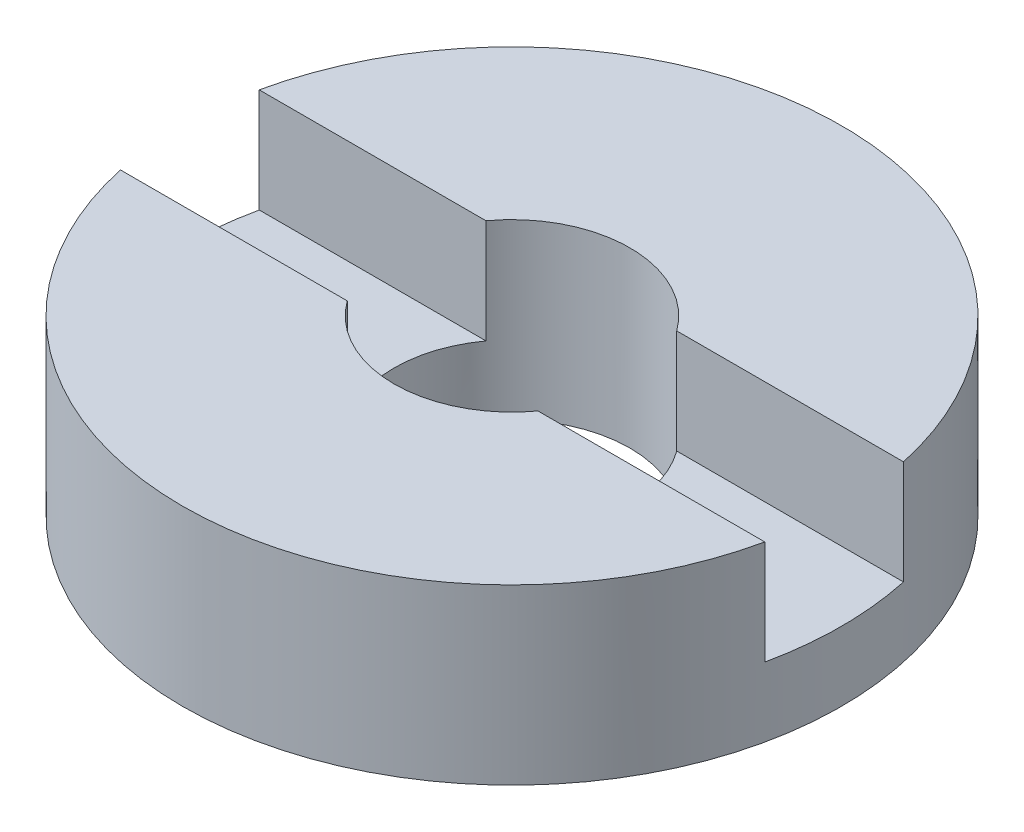
SolidWorks part; units mm, degrees
ref_plane "前视基准面" through (0, 0, 0) normal (0, 0, 1) x (1, 0, 0)
ref_plane "上视基准面" through (0, 0, 0) normal (0, 1, 0) x (1, 0, 0)
ref_plane "右视基准面" through (0, 0, 0) normal (1, 0, 0) x (0, 0, -1)
sketch "草图1" plane through (0, 0, 0) normal (0, 0, 1) x (1, 0, 0)
  line L0 (0, 56.2608) -> (0, -99.1922) construction
  line L1 (1.7, -1.9642) -> (4.75, -1.9642)
  line L4 (4.75, -1.9642) -> (4.75, -4.4642)
  line L5 (1.7, -4.4642) -> (1.7, -1.9642)
  line L7 (1.7, -4.4642) -> (4.75, -4.4642)
  dimension "D1" = 2.5
  dimension "D2" = 4.75
  dimension "D3" = 1.7
revolve "旋转1" add sketch "草图1" angle 360 about L0
cosmetic thread "装饰螺纹线1" parameters "D2"=8.5
sketch "草图2" plane through (0, -1.9642, 0) normal (0, 1, 0) x (1, 0, 0)
  line L0 (-28.67, 0) -> (29.9422, 0) construction
  line L2 (-26.8525, 1) -> (26.8525, 1)
  line L3 (-26.8525, 1) -> (-26.8525, -1)
  line L4 (-26.8525, -1) -> (26.8525, -1)
  line L5 (26.8525, 1) -> (26.8525, -1)
  line L6 (-26.8525, 1) -> (26.8525, -1) construction
  line L7 (-26.8525, -1) -> (26.8525, 1) construction
  point P3 (0, 0)
  dimension "D1" = 2
extrude "切除-拉伸1" cut sketch "草图2" against normal blind 1.5
